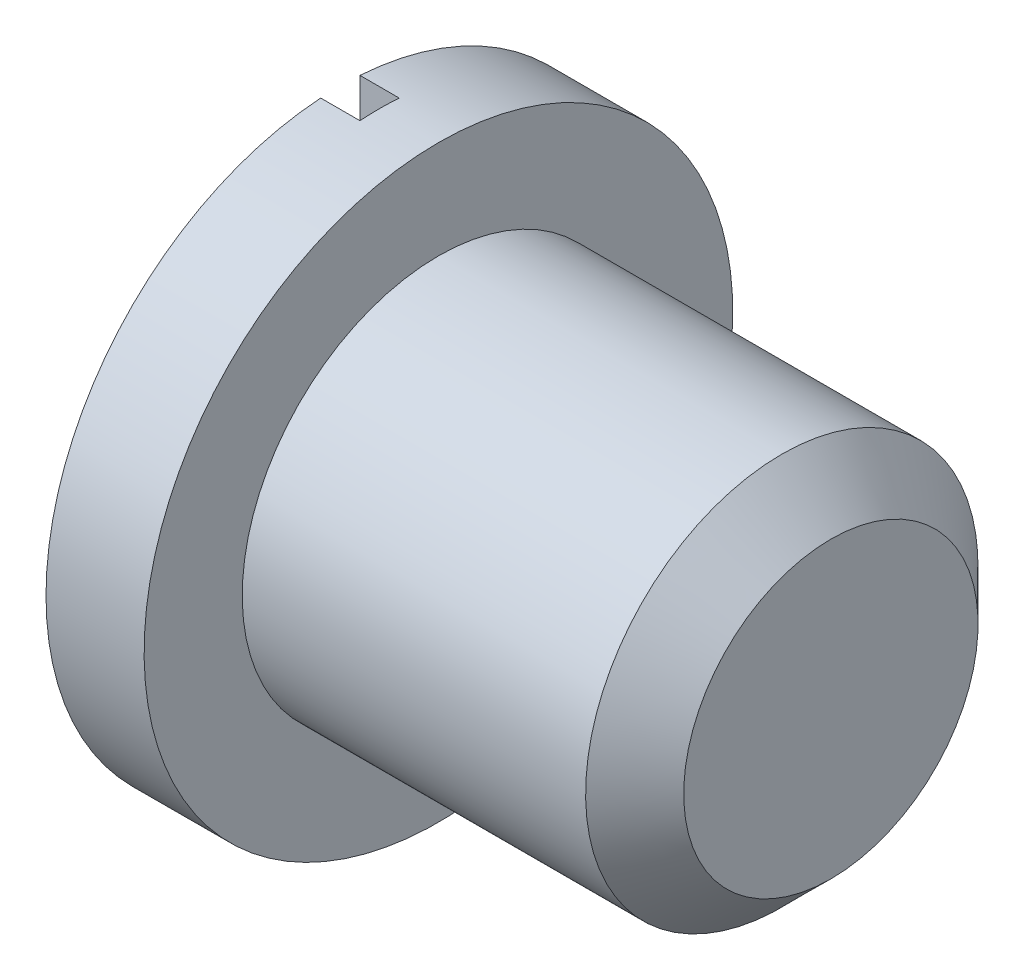
SolidWorks part; units mm, degrees
ref_plane "Front Plane" through (0, 0, 0) normal (0, 0, 1) x (1, 0, 0)
ref_plane "Top Plane" through (0, 0, 0) normal (0, 1, 0) x (1, 0, 0)
ref_plane "Right Plane" through (0, 0, 0) normal (1, 0, 0) x (0, 0, -1)
sketch "Croquis1" plane through (0, 0, 0) normal (0, 0, 1) x (1, 0, 0)
  line L0 (0, 0) -> (0, 0.75)
  line L1 (0, 0.75) -> (0.25, 0.75)
  line L2 (0.25, 0.75) -> (0.25, 0.5)
  line L3 (0.25, 0.5) -> (1.25, 0.5)
  line L4 (1.25, 0.5) -> (1.25, 0)
  line L5 (1.25, 0) -> (0, 0)
  dimension "D1" = 0.75
  dimension "D2" = 0.25
  dimension "D3" = 1.25
  dimension "D4" = 0.5
revolve "Revolución1" add sketch "Croquis1" angle 360 about L5
cosmetic thread "Rosca cosmética1" parameters "D2"=0.75
chamfer "Chaflán1" distance 0.125 angle 45 1 edges at (1.25, 0.5, 0)
sketch "Croquis5" plane through (0, 0, 0) normal (-1, 0, 0) x (0, 0, 1)
  line L2 (-0.05, 0.7483) -> (-0.05, -0.7483)
  line L4 (0.05, 0.7483) -> (0.05, -0.7483)
  arc A0 (0.05, 0.7483) -> (-0.05, 0.7483) centre (0, 0) ccw
  circle A1 centre (0, 0) radius 0.75 construction
  arc A2 (-0.05, -0.7483) -> (0.05, -0.7483) centre (0, 0) ccw
  dimension "D1" = 0.1
extrude "Cortar-Extruir6" cut sketch "Croquis5" against normal blind 0.1
